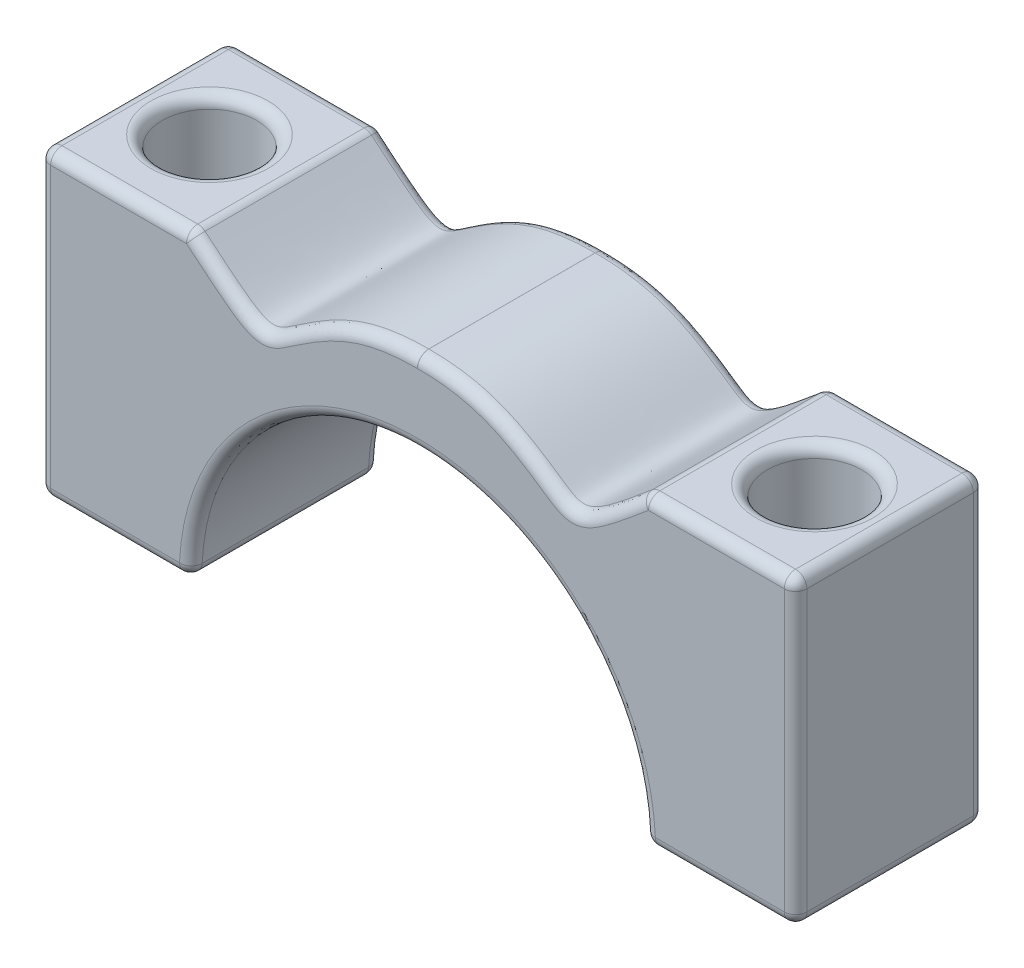
SolidWorks part; units mm, degrees
ref_plane "Front Plane" through (0, 0, 0) normal (0, 0, 1) x (1, 0, 0)
ref_plane "Top Plane" through (0, 0, 0) normal (0, 1, 0) x (1, 0, 0)
ref_plane "Right Plane" through (0, 0, 0) normal (1, 0, 0) x (0, 0, -1)
sketch "Sketch1" plane through (0, 0, 0) normal (0, 0, 1) x (1, 0, 0)
  line L0 (-66.518, 291.1867) -> (465.1295, 291.1867) construction
  line L1 (-188.4446, 82.1731) -> (-188.4446, 90.1731)
  line L2 (-188.4446, 90.1731) -> (-184.4446, 90.1731)
  line L3 (-184.4446, 82.1731) -> (-188.4446, 82.1731)
  line L4 (-172.4446, 90.1731) -> (-168.4446, 90.1731)
  line L5 (-168.4446, 90.1731) -> (-168.4446, 82.1731)
  line L6 (-168.4446, 82.1731) -> (-172.4446, 82.1731)
  line L8 (-178.4446, 93.3685) -> (-178.4446, 77.9821) construction
  arc A1 (-172.4446, 82.1731) -> (-184.4446, 82.1731) centre (-178.4446, 82.1731) ccw
  spline S0 degree 3 poles (-184.4446, 90.1731) (-182.7105, 88.7188) (-182.5803, 88.6718) (-180.4886, 90.2006) (-178.9734, 90.3688) (-178.4446, 90.3665) knots 0 0 0 0 0.237143 0.406825 0.49839 0.49839 0.49839 0.49839
  spline S1 degree 3 poles (-172.4446, 90.1731) (-174.1787, 88.7188) (-174.3089, 88.6718) (-176.4006, 90.2006) (-177.9158, 90.3688) (-178.4446, 90.3665) knots 0 0 0 0 0.237143 0.406825 0.49839 0.49839 0.49839 0.49839
  dimension "D1" = 20
  dimension "D2" = 8
extrude "Boss-Extrude1" add sketch "Sketch1" along normal blind 5
sketch "Sketch2" plane through (0, 90.1731, 0) normal (0, 1, 0) x (1, 0, 0)
  line L0 (-184.4446, 0) -> (-188.4446, 0) construction
  line L5 (-188.4446, -5) -> (-188.4446, 0) construction
  circle A0 centre (-186.4446, -2.5) radius 1.25
  circle A1 centre (-170.4446, -2.5) radius 1.25
  point P8 (-188.4446, -2.5)
  dimension "D1" = 2.5
  dimension "D2" = 16
  dimension "D3" = 2
extrude "Cut-Extrude2" cut sketch "Sketch2" against normal up to next contours A1 | A0
fillet "Fillet1" radius 0.3 31 edges at (-170.4446, 82.1731, 3.75) (-186.4446, 82.1731, 3.75) (-188.4446, 82.1731, 2.5) (-168.4446, 82.1731, 2.5) (-170.4446, 82.1731, 0) (-168.4446, 86.1731, 0) (-188.4446, 86.1731, 0) (-186.4446, 82.1731, 0) (-168.4446, 90.1731, 2.5) (-170.4446, 90.1731, 0) (-170.4446, 90.1731, 3.75) (-188.4446, 90.1731, 2.5) (-186.4446, 90.1731, 0) (-186.4446, 90.1731, 3.75) (-184.4446, 90.1731, 2.5) (-172.4446, 90.1731, 2.5) (-178.4446, 90.3665, 2.5) (-188.4446, 86.1731, 5) (-186.4446, 90.1731, 5) (-170.4446, 90.1731, 5) (-168.4446, 86.1731, 5) (-170.4446, 82.1731, 5) (-186.4446, 82.1731, 5) (-172.4446, 82.1731, 2.5) (-184.4446, 82.1731, 2.5) (-178.4446, 88.1731, 0) (-178.4446, 88.1731, 5)
